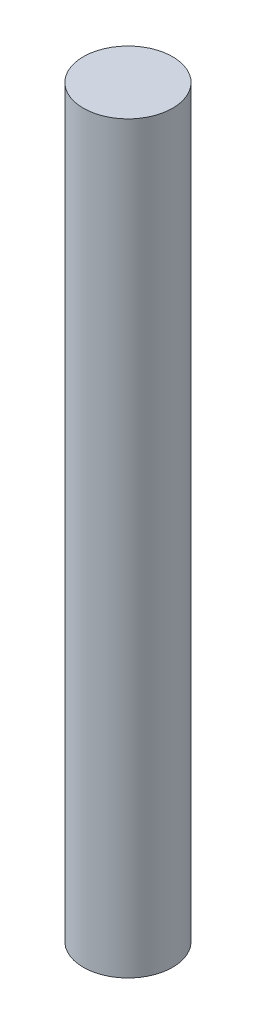
SolidWorks part; units mm, degrees
ref_plane "Front Plane" through (0, 0, 0) normal (0, 0, 1) x (1, 0, 0)
ref_plane "Top Plane" through (0, 0, 0) normal (0, 1, 0) x (1, 0, 0)
ref_plane "Right Plane" through (0, 0, 0) normal (1, 0, 0) x (0, 0, -1)
sketch "Sketch1" plane through (0, 0, 0) normal (0, 1, 0) x (1, 0, 0)
  circle A0 centre (0, 0) radius 9.525
  dimension "D1" = 19.05
extrude "Boss-Extrude1" add sketch "Sketch1" along normal blind 158.75
